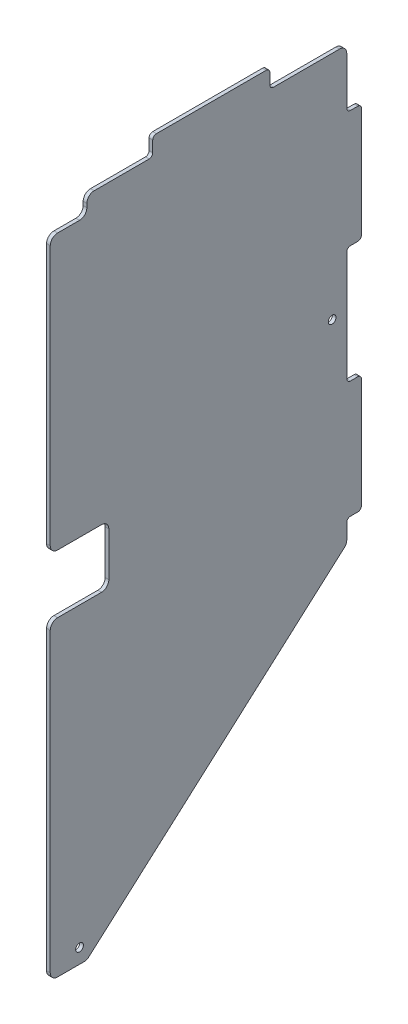
SolidWorks part; units mm, degrees
material "PC High Viscosity"
ref_plane "Front Plane" through (0, 0, 0) normal (0, 0, 1) x (1, 0, 0)
ref_plane "Top Plane" through (0, 0, 0) normal (0, 1, 0) x (1, 0, 0)
ref_plane "Right Plane" through (0, 0, 0) normal (1, 0, 0) x (0, 0, -1)
sketch "Sketch1" plane through (0, 0, 0) normal (1, 0, 0) x (0, 0, -1)
  line L0 (0, 0) -> (0, -574.675)
  line L1 (0, -574.675) -> (31.75, -574.675)
  line L2 (257.175, -374.65) -> (257.175, 0)
  line L3 (0, 0) -> (257.175, 0)
  line L4 (257.175, -374.65) -> (31.75, -574.675)
  dimension "D1" = 257.175
  dimension "D3" = 574.675
  dimension "D4" = 374.65
  dimension "D5" = 31.75
extrude "Boss-Extrude1" add sketch "Sketch1" along normal blind 3.175
sketch "Sketch2" plane through (3.175, 0, 0) normal (1, 0, 0) x (0, 0, -1)
  line L3 (0, 0) -> (0, -574.675) construction
  line L4 (0, -574.675) -> (31.75, -574.675) construction
  circle A2 centre (25.4, -561.975) radius 3.3655
  dimension "D1" = 6.731
  dimension "D6" = 12.7
  dimension "D7" = 25.4
extrude "Cut-Extrude1" cut sketch "Sketch2" against normal through all
sketch "Sketch8" plane through (3.175, 0, 0) normal (1, 0, 0) x (0, 0, -1)
  line L0 (0, 0) -> (0, -574.675) construction
  line L1 (0, -254) -> (50.8, -254)
  line L2 (0, -254) -> (0, -304.8)
  line L3 (0, -304.8) -> (50.8, -304.8)
  line L4 (50.8, -254) -> (50.8, -304.8)
  line L5 (257.175, 0) -> (0, 0) construction
  dimension "D1" = 254
  dimension "D2" = 50.8
  dimension "D3" = 50.8
extrude "Cut-Extrude9" cut sketch "Sketch8" against normal through all
fillet "Fillet2" radius 6.35 4 edges at (1.5875, -304.8, 0) (1.5875, -304.8, -50.8) (1.5875, -254, -50.8) (1.5875, -254, 0)
sketch "Sketch9" plane through (3.175, 0, 0) normal (1, 0, 0) x (0, 0, -1)
  line L0 (257.175, 0) -> (0, 0) construction
  line L1 (88.9, 0) -> (190.5, 0)
  line L2 (88.9, 0) -> (88.9, 15.875)
  line L3 (88.9, 15.875) -> (190.5, 15.875)
  line L4 (190.5, 0) -> (190.5, 15.875)
  line L5 (257.175, -374.65) -> (257.175, 0) construction
  line L6 (257.175, -50.8) -> (269.875, -50.8)
  line L7 (257.175, -50.8) -> (257.175, -152.4)
  line L8 (257.175, -152.4) -> (269.875, -152.4)
  line L9 (269.875, -50.8) -> (269.875, -152.4)
  line L10 (0, 0) -> (0, -247.65) construction
  line L11 (257.175, -254) -> (269.875, -254)
  line L12 (257.175, -254) -> (257.175, -355.6)
  line L13 (257.175, -355.6) -> (269.875, -355.6)
  line L14 (269.875, -254) -> (269.875, -355.6)
  point P18 (139.7, 15.875)
  dimension "D1" = 12.7
  dimension "D2" = 50.8
  dimension "D3" = 254
  dimension "D4" = 101.6
  dimension "D5" = 15.875
  dimension "D6" = 139.7
  dimension "D7" = 101.6
extrude "Boss-Extrude2" add sketch "Sketch9" against normal up to surface (3.175 mm away) up to face at (0, -561.975, -28.7655)
fillet "Fillet3" radius 3.175 12 edges at (1.5875, -355.6, -269.875) (1.5875, -355.6, -257.175) (1.5875, -254, -269.875) (1.5875, -254, -257.175) (1.5875, -152.4, -269.875) (1.5875, -152.4, -257.175) (1.5875, -50.8, -269.875) (1.5875, -50.8, -257.175) (1.5875, 15.875, -190.5) (1.5875, 0, -190.5) (1.5875, 15.875, -88.9) (1.5875, 0, -88.9)
sketch "Sketch10" plane through (3.175, 0, 0) normal (1, 0, 0) x (0, 0, -1)
  line L1 (0, 0) -> (31.75, 0)
  line L2 (0, 0) -> (0, -15.875)
  line L3 (0, -15.875) -> (31.75, -15.875)
  line L4 (31.75, 0) -> (31.75, -15.875)
  dimension "D1" = 31.75
  dimension "D2" = 15.875
extrude "Cut-Extrude12" cut sketch "Sketch10" against normal through all
fillet "Fillet4" radius 6.35 7 edges at (1.5875, -574.675, 0) (1.5875, -574.675, -31.75) (1.5875, -374.65, -257.175) (1.5875, 0, -257.175) (1.5875, 0, -31.75) (1.5875, -15.875, -31.75) (1.5875, -15.875, 0)
hole_wizard "17/64 (0.26563) Diameter Hole1" positions "Sketch11" profile "Sketch12" hole size "17/64" standard "ANSI Inch" end condition through all
sketch "Sketch11" plane through (3.175, 0, 0) normal (1, 0, 0) x (0, 0, -1)
  line L0 (250.825, 0) -> (193.675, 0) construction
  line L1 (257.175, -250.825) -> (257.175, -155.575) construction
  point P0 (244.475, -200.025)
  dimension "D1" = 200.025
  dimension "D2" = 12.7
sketch "Sketch12" plane through (3.175, -200.025, -244.475) normal (0, 1, 0) x (0, 0, -1)
  line L0 (0, 0) -> (0, 3.175)
  line L1 (0, 3.175) -> (3.3735, 3.175)
  line L2 (3.3735, 3.175) -> (3.3735, 0)
  line L5 (3.3735, 0) -> (0, 0)
  line L11 (0, -6.35) -> (0, 107.95) construction
  dimension "Thru Hole Dia." = 6.747
  dimension "Thru Hole Depth" = 3.175
